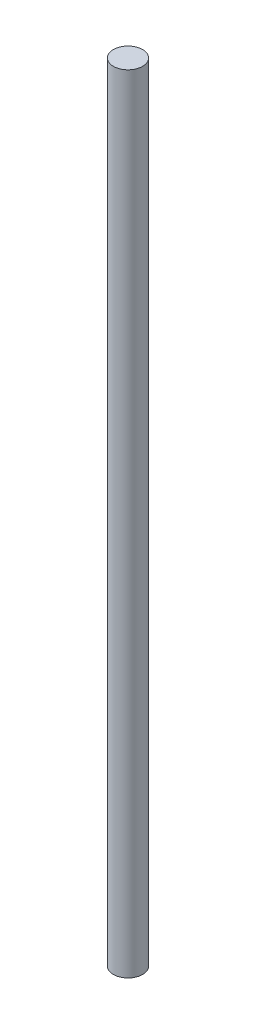
SolidWorks part; units mm, degrees
ref_plane "Front Plane" through (0, 0, 0) normal (0, 0, 1) x (1, 0, 0)
ref_plane "Top Plane" through (0, 0, 0) normal (0, 1, 0) x (1, 0, 0)
ref_plane "Right Plane" through (0, 0, 0) normal (1, 0, 0) x (0, 0, -1)
sketch "Sketch1" plane through (0, 0, 0) normal (0, 1, 0) x (1, 0, 0)
  circle A0 centre (0, 0) radius 914.4
  dimension "D1" = 1828.8
extrude "Boss-Extrude1" add sketch "Sketch1" along normal blind 49276
